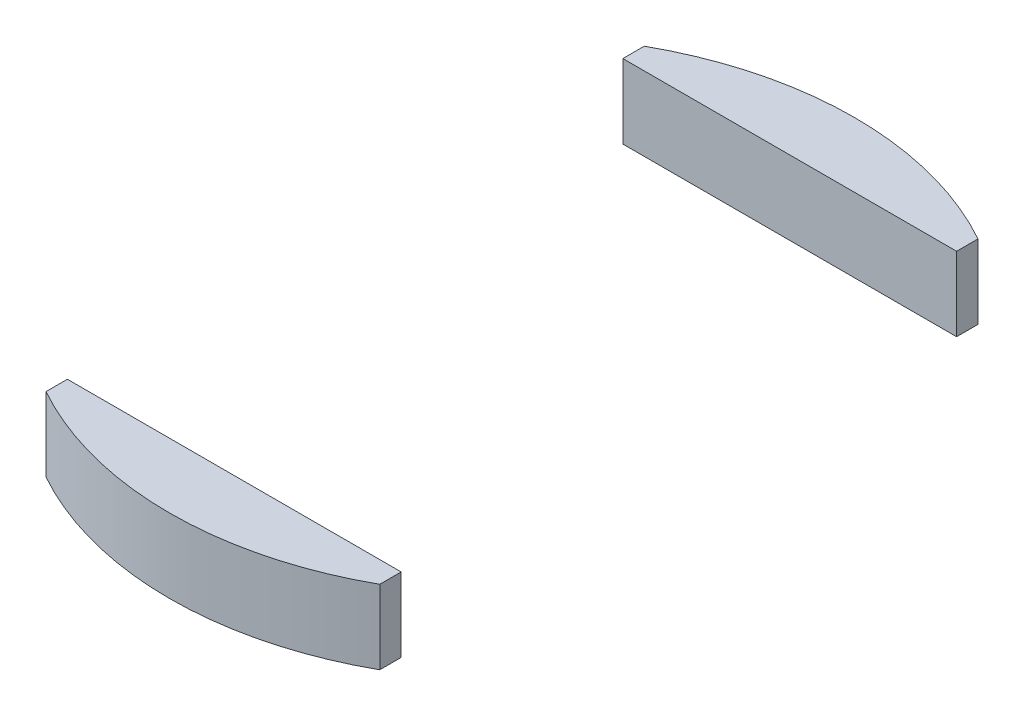
SolidWorks part; units mm, degrees
ref_plane "Front Plane" through (0, 0, 0) normal (0, 0, 1) x (1, 0, 0)
ref_plane "Top Plane" through (0, 0, 0) normal (0, 1, 0) x (1, 0, 0)
ref_plane "Right Plane" through (0, 0, 0) normal (1, 0, 0) x (0, 0, -1)
sketch "Sketch1" plane through (0, 0, 0) normal (0, 1, 0) x (1, 0, 0)
  line L0 (-17.5, 0) -> (17.5, 0) construction
  line L1 (0, 17.5) -> (0, 15) construction
  line L2 (-9.0139, 15) -> (9.0139, 15)
  line L3 (-9.0139, 15) -> (-9.0139, 16.1555)
  line L4 (9.0139, 15) -> (9.0139, 16.1555)
  line L5 (9.0139, -15) -> (9.0139, -16.1555)
  line L6 (-9.0139, -15) -> (-9.0139, -16.1555)
  line L7 (-9.0139, -15) -> (9.0139, -15)
  circle A0 centre (0, 0) radius 17.5
  circle A1 centre (0, 0) radius 18.5
  dimension "D1" = 37
  dimension "D2" = 35
  dimension "D3" = 2.5
extrude "Boss-Extrude1" add sketch "Sketch1" along normal blind 4 contours L2 A0 | L4 A1 L3 A0 | L7 A0 | L6 A1 L5 A0
